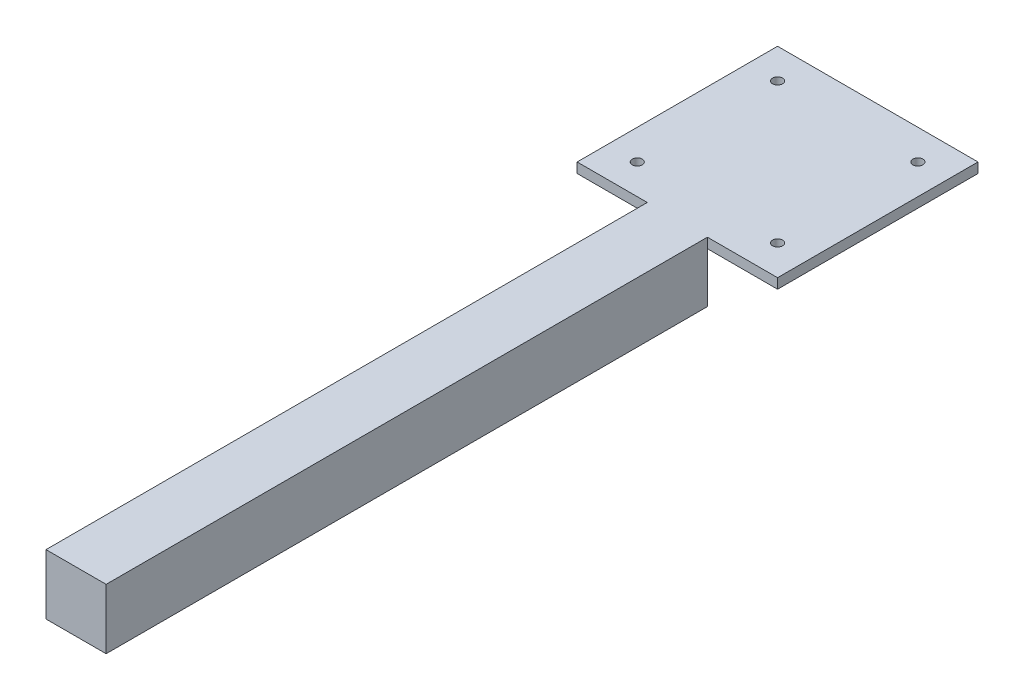
SolidWorks part; units mm, degrees
ref_plane "Front Plane" through (0, 0, 0) normal (0, 0, 1) x (1, 0, 0)
ref_plane "Top Plane" through (0, 0, 0) normal (0, 1, 0) x (1, 0, 0)
ref_plane "Right Plane" through (0, 0, 0) normal (1, 0, 0) x (0, 0, -1)
sketch "Sketch1" plane through (0, 0, 0) normal (0, 0, 1) x (1, 0, 0)
  line L1 (15, -15) -> (-15, -15)
  line L2 (15, -15) -> (15, 15)
  line L3 (15, 15) -> (-15, 15)
  line L4 (-15, -15) -> (-15, 15)
  line L5 (15, -15) -> (-15, 15) construction
  line L6 (15, 15) -> (-15, -15) construction
  point P0 (0, 0)
  dimension "D1" = 30
  dimension "D2" = 30
extrude "Boss-Extrude1" add sketch "Sketch1" along normal blind 300
sketch "Sketch2" plane through (0, 15, 0) normal (0, 1, 0) x (1, 0, 0)
  line L1 (-50, 0) -> (50, 0)
  line L2 (-50, 0) -> (-50, 100)
  line L3 (-50, 100) -> (50, 100)
  line L4 (50, 0) -> (50, 100)
  point P4 (0, 100)
  dimension "D1" = 100
  dimension "D2" = 100
extrude "Boss-Extrude2" add sketch "Sketch2" against normal blind 5
sketch "Sketch3" plane through (0, 15, 0) normal (0, 1, 0) x (1, 0, 0)
  line L0 (0, 0) -> (0, 100) construction
  line L1 (50, 100) -> (-50, 100) construction
  line L2 (-50, 50) -> (50, 50) construction
  line L3 (-50, 100) -> (-50, 0) construction
  line L4 (50, 0) -> (50, 100) construction
  circle A0 centre (-35, 15) radius 2.5
  circle A1 centre (35, 15) radius 2.5
  circle A2 centre (-35, 85) radius 2.5
  circle A3 centre (35, 85) radius 2.5
  dimension "D1" = 70
  dimension "D2" = 70
  dimension "D3" = 5
extrude "Cut-Extrude1" cut sketch "Sketch3" against normal up to next
